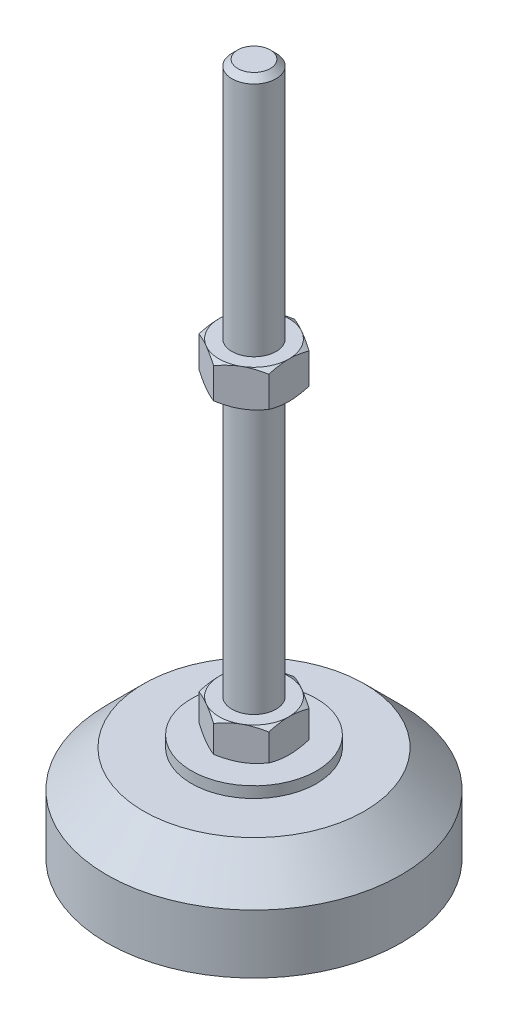
SolidWorks part; units mm, degrees
ref_plane "Спереди" through (0, 0, 0) normal (0, 0, 1) x (1, 0, 0)
ref_plane "Сверху" through (0, 0, 0) normal (0, 1, 0) x (1, 0, 0)
ref_plane "Справа" through (0, 0, 0) normal (1, 0, 0) x (0, 0, -1)
sketch "Эскиз1" plane through (0, 0, 0) normal (0, 0, 1) x (1, 0, 0)
  line L0 (0, 0) -> (-40, 0)
  line L3 (-40, 0) -> (-40, 16)
  line L5 (-17, 29) -> (-6, 29)
  line L12 (-6, 38) -> (-6, 186.4)
  line L13 (-6, 186.4) -> (-4.4, 188)
  line L14 (-4.4, 188) -> (0, 188)
  line L15 (0, 188) -> (0, 0) construction
  line L16 (-6, 29) -> (0, 29) construction
  line L17 (0, 0) -> (0, 188)
  line L18 (0, 0) -> (0, -7.9595) construction
  line L19 (-6, 38) -> (-6, 29)
  line L20 (-17, 29) -> (-17, 26)
  line L21 (-17, 26) -> (-30, 26)
  line L22 (-30, 26) -> (-40, 16)
  point P8 (-6, 112.2)
  point P23 (-11.5, 29)
  dimension "D1" = 12
  dimension "D2" = 29
  dimension "D3" = 9
  dimension "D4" = 80
  dimension "D5" = 6
  dimension "D6" = 1.6
  dimension "D7" = 45
  dimension "D8" = 34
  dimension "D10" = 150
  dimension "D11" = 16
  dimension "D12" = 45
  dimension "D13" = 3
revolve "Повернуть1" add sketch "Эскиз1" angle 360 about L17
sketch "Эскиз2" plane through (0, 29, 0) normal (0, 1, 0) x (1, 0, 0)
  line L1 (0, 10.9697) -> (-9.5, 5.4848)
  line L2 (-9.5, 5.4848) -> (-9.5, -5.4848)
  line L3 (-9.5, -5.4848) -> (0, -10.9697)
  line L4 (0, -10.9697) -> (9.5, -5.4848)
  line L5 (9.5, -5.4848) -> (9.5, 5.4848)
  line L6 (9.5, 5.4848) -> (0, 10.9697)
  circle A0 centre (0, 0) radius 9.5 construction
  dimension "D1" = 19
extrude "Бобышка-Вытянуть1" add sketch "Эскиз2" along normal up to vertex (9 mm away) up to point (-6, 38, 0)
ref_plane "Плоскость1" through (0, 112.2, 0) normal (0, 1, 0) x (1, 0, 0)
sketch "Эскиз3" plane through (0, 112.2, 0) normal (0, 1, 0) x (1, 0, 0)
  line L6 (9.5, 5.4848) -> (0, 10.9697)
  line L7 (0, 10.9697) -> (-9.5, 5.4848)
  line L8 (-9.5, 5.4848) -> (-9.5, -5.4848)
  line L9 (-9.5, -5.4848) -> (0, -10.9697)
  line L10 (0, -10.9697) -> (9.5, -5.4848)
  line L11 (9.5, -5.4848) -> (9.5, 5.4848)
  line L12 (9.5, 5.4848) -> (0, 10.9697)
  line L13 (0, 10.9697) -> (-9.5, 5.4848)
  line L14 (-9.5, 5.4848) -> (-9.5, -5.4848)
  line L15 (-9.5, -5.4848) -> (0, -10.9697)
  line L16 (0, -10.9697) -> (9.5, -5.4848)
  line L17 (9.5, -5.4848) -> (9.5, 5.4848)
  dimension "D1" = 0
extrude "Бобышка-Вытянуть2" add sketch "Эскиз3" along normal blind 10
sketch "Эскиз4" plane through (0, 0, 0) normal (0, 0, 1) x (1, 0, 0)
  line L0 (-9.5, 122.2) -> (-18.1603, 117.2)
  line L1 (-18.1603, 117.2) -> (-18.1603, 122.2)
  line L2 (-18.1603, 122.2) -> (-9.5, 122.2)
  line L3 (-18.1603, 117.2) -> (-9.5, 112.2)
  line L4 (50, 112.2) -> (-50, 112.2) construction
  line L5 (-9.5, 112.2) -> (-18.1603, 112.2)
  line L6 (-18.1603, 112.2) -> (-18.1603, 117.2)
  line L7 (-9.5, 122.2) -> (-9.5, 112.2) construction
  line L8 (-9.5, 38) -> (-17.2942, 38)
  line L9 (-17.2942, 38) -> (-17.2942, 33.5)
  line L10 (-17.2942, 33.5) -> (-9.5, 38)
  line L11 (-9.5, 29) -> (-17.2942, 33.5)
  line L12 (-17.2942, 33.5) -> (-17.2942, 29)
  line L13 (-17.2942, 29) -> (-9.5, 29)
  line L14 (0, 188) -> (0, 96.3793) construction
  dimension "D1" = 30
  dimension "D2" = 30
revolve "Вырез-Повернуть2" cut sketch "Эскиз4" angle 360 about L14
